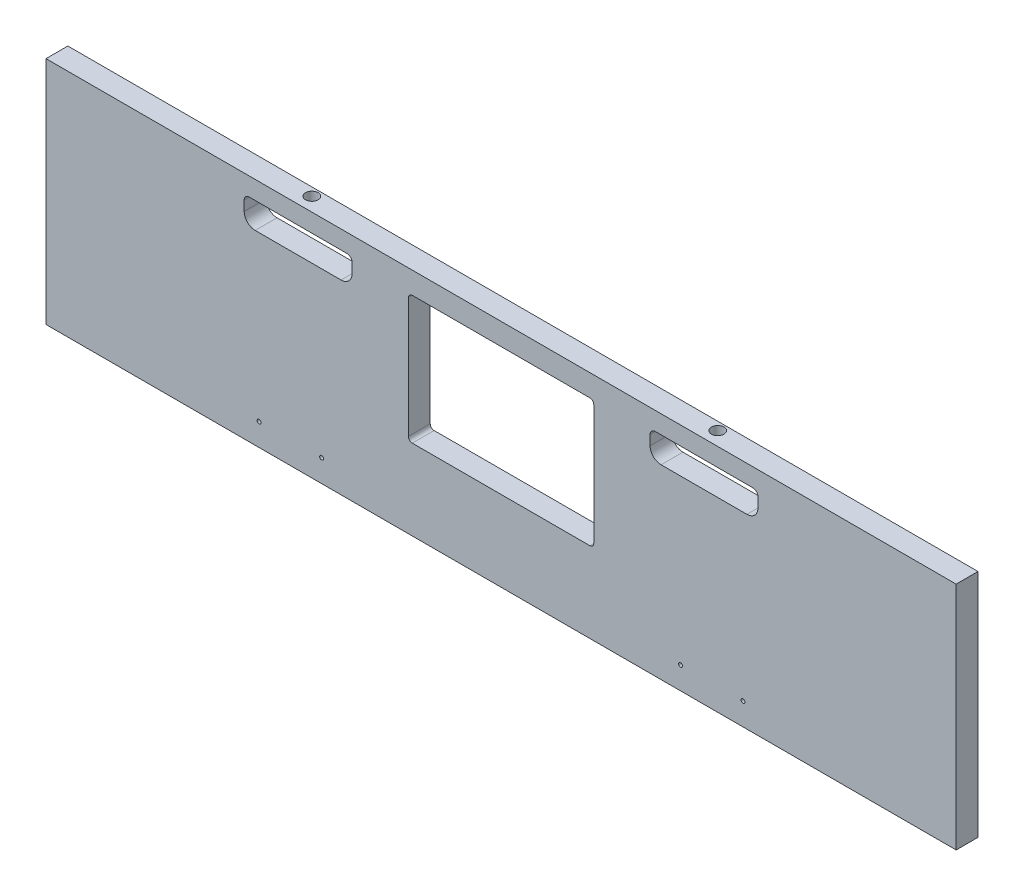
SolidWorks part; units mm, degrees
material "Pine"
ref_plane "Front Plane" through (0, 0, 0) normal (0, 0, 1) x (1, 0, 0)
ref_plane "Top Plane" through (0, 0, 0) normal (0, 1, 0) x (1, 0, 0)
ref_plane "Right Plane" through (0, 0, 0) normal (1, 0, 0) x (0, 0, -1)
sketch "Sketch1" plane through (0, 0, 0) normal (0, 0, 1) x (1, 0, 0)
  line L0 (-163.9887, -5335.905) -> (-163.9887, -5432.425)
  line L1 (-102.87, -5350.891) -> (-33.02, -5350.891)
  line L2 (-111.8235, -5341.9375) -> (-111.8235, -5334)
  line L3 (-24.0665, -5341.9375) -> (-24.0665, -5334)
  line L4 (-298.9262, -5332.73) -> (-167.1637, -5332.73)
  line L5 (-167.1637, -5435.6) -> (-298.9262, -5435.6)
  line L6 (-302.1012, -5432.425) -> (-302.1012, -5335.905)
  line L7 (-107.6325, -5329.809) -> (-28.2575, -5329.809)
  line L8 (174.9425, -5308.6) -> (174.9425, -5581.65)
  line L9 (449.2625, -5413.1661) -> (449.2625, -5421.9659)
  line L10 (595.3125, -5421.9659) -> (595.3125, -5413.1661)
  line L11 (839.47, -5509.5521) -> (839.47, -5307.6729)
  line L12 (839.47, -5307.6729) -> (863.6, -5307.6729)
  line L13 (839.47, -5509.5521) -> (863.6, -5509.5521)
  line L14 (863.6, -5509.5521) -> (863.6, -5307.6729)
  line L15 (-354.2665, -5341.9375) -> (-354.2665, -5334)
  line L16 (-100.8856, -5889.625) -> (-50.0856, -5889.625)
  line L17 (-104.0606, -5969) -> (-104.0606, -5892.8)
  line L18 (-46.9106, -5892.8) -> (-46.9106, -5969)
  line L19 (-50.0856, -5972.175) -> (-100.8856, -5972.175)
  line L20 (-100.8856, -5848.35) -> (-50.0856, -5848.35)
  line L21 (857.25, -5502.275) -> (157.1625, -5575.3)
  line L22 (857.25, -5314.95) -> (857.25, -5502.275)
  line L23 (157.1625, -5314.95) -> (157.1625, -5575.3)
  line L24 (857.25, -5314.95) -> (157.1625, -5314.95)
  line L25 (150.8125, -5308.6) -> (174.9425, -5308.6)
  line L26 (174.9425, -5581.65) -> (150.8125, -5581.65)
  line L27 (137.16, -5314.95) -> (137.16, -5502.275)
  line L28 (150.8125, -5581.65) -> (150.8125, -5308.6)
  line L29 (590.8224, -5408.676) -> (453.7526, -5408.676)
  line L30 (453.7526, -5426.456) -> (590.8224, -5426.456)
  line L31 (137.16, -6013.45) -> (137.16, -5867.4)
  line L32 (150.8125, -5746.75) -> (150.8125, -6019.8)
  line L33 (143.51, -5639.9938) -> (143.51, -5654.294)
  line L34 (590.8224, -5919.724) -> (453.7526, -5919.724)
  line L35 (453.7526, -5901.944) -> (590.8224, -5901.944)
  line L36 (449.2625, -5915.2339) -> (449.2625, -5906.4341)
  line L37 (174.9425, -6019.8) -> (174.9425, -5746.75)
  line L38 (595.3125, -5906.4341) -> (595.3125, -5915.2339)
  line L39 (839.47, -5818.8479) -> (839.47, -6020.7271)
  line L40 (839.47, -5818.8479) -> (863.6, -5818.8479)
  line L41 (863.6, -5818.8479) -> (863.6, -6020.7271)
  line L42 (839.47, -6020.7271) -> (863.6, -6020.7271)
  line L43 (-155.8782, -5867.4) -> (-603.25, -5867.4)
  line L44 (-433.07, -5350.891) -> (-363.22, -5350.891)
  line L45 (-437.8325, -5329.809) -> (-358.4575, -5329.809)
  line L46 (889, -6045.2) -> (-635, -6045.2)
  line L47 (-635, -5283.2) -> (889, -5283.2)
  line L48 (-635, -6045.2) -> (-635, -5283.2)
  line L49 (889, -5283.2) -> (889, -6045.2)
  line L50 (137.16, -5502.275) -> (-603.25, -5502.275)
  line L51 (-603.25, -5314.95) -> (137.16, -5314.95)
  line L52 (143.51, -5654.294) -> (-609.6, -5654.294)
  line L53 (-609.6, -5639.9938) -> (143.51, -5639.9938)
  line L54 (137.16, -5536.0062) -> (-603.25, -5536.0062)
  line L55 (-603.25, -5794.375) -> (137.16, -5794.375)
  line L56 (-603.25, -6013.45) -> (137.16, -6013.45)
  line L57 (-603.25, -5536.0062) -> (-603.25, -5794.375)
  line L58 (137.16, -5794.375) -> (137.16, -5536.0062)
  line L59 (-609.6, -5654.294) -> (-609.6, -5639.9938)
  line L60 (-603.25, -5867.4) -> (-603.25, -6013.45)
  line L61 (-603.25, -5314.95) -> (-603.25, -5502.275)
  line L62 (-442.0235, -5341.9375) -> (-442.0235, -5334)
  line L63 (857.25, -5826.125) -> (157.1625, -5753.1)
  line L64 (857.25, -6013.45) -> (857.25, -5826.125)
  line L65 (157.1625, -6013.45) -> (157.1625, -5753.1)
  line L66 (857.25, -6013.45) -> (157.1625, -6013.45)
  line L67 (174.9425, -5746.75) -> (150.8125, -5746.75)
  line L68 (150.8125, -6019.8) -> (174.9425, -6019.8)
  line L69 (137.16, -5867.4) -> (4.907, -5867.4)
  circle A0 centre (-36.195, -5484.0124) radius 1.5875
  arc A1 (-298.9262, -5332.73) -> (-302.1012, -5335.905) centre (-298.9262, -5335.905) ccw
  arc A2 (-302.1012, -5432.425) -> (-298.9262, -5435.6) centre (-298.9262, -5432.425) ccw
  arc A3 (-163.9887, -5335.905) -> (-167.1637, -5332.73) centre (-167.1637, -5335.905) ccw
  arc A4 (-167.1637, -5435.6) -> (-163.9887, -5432.425) centre (-167.1637, -5432.425) ccw
  arc A5 (-111.8235, -5341.9375) -> (-102.87, -5350.891) centre (-102.87, -5341.9375) ccw
  arc A6 (-107.6325, -5329.809) -> (-111.8235, -5334) centre (-107.6325, -5334) ccw
  circle A7 centre (166.0525, -5444.6613) radius 1.5875
  circle A8 centre (166.0525, -5358.1871) radius 1.5875
  circle A9 centre (471.4875, -5417.566) radius 1.5875
  arc A10 (453.7526, -5408.676) -> (449.2625, -5413.1661) centre (451.5076, -5410.9211) ccw
  arc A11 (449.2625, -5421.9659) -> (453.7526, -5426.456) centre (451.5076, -5424.2109) ccw
  circle A12 centre (522.2875, -5417.566) radius 1.5875
  circle A13 centre (573.0875, -5417.566) radius 1.5875
  arc A14 (590.8224, -5426.456) -> (595.3125, -5421.9659) centre (593.0674, -5424.2109) ccw
  arc A15 (595.3125, -5413.1661) -> (590.8224, -5408.676) centre (593.0674, -5410.9211) ccw
  circle A16 centre (848.36, -5471.8269) radius 1.5875
  circle A17 centre (848.36, -5409.0762) radius 1.5875
  circle A18 centre (848.36, -5346.3254) radius 1.5875
  arc A19 (-363.22, -5350.891) -> (-354.2665, -5341.9375) centre (-363.22, -5341.9375) ccw
  arc A20 (-354.2665, -5334) -> (-358.4575, -5329.809) centre (-358.4575, -5334) ccw
  arc A21 (-24.0665, -5334) -> (-28.2575, -5329.809) centre (-28.2575, -5334) ccw
  arc A22 (-33.02, -5350.891) -> (-24.0665, -5341.9375) centre (-33.02, -5341.9375) ccw
  circle A23 centre (-86.995, -5484.0124) radius 1.5875
  circle A24 centre (-333.4544, -5894.07) radius 2.54
  circle A25 centre (-333.4544, -5994.4) radius 2.54
  arc A26 (-104.0606, -5969) -> (-100.8856, -5972.175) centre (-100.8856, -5969) ccw
  arc A27 (-50.0856, -5972.175) -> (-46.9106, -5969) centre (-50.0856, -5969) ccw
  arc A28 (-100.8856, -5848.35) -> (-128.3819, -5857.875) centre (-100.8856, -5892.8) ccw
  arc A29 (-155.8782, -5867.4) -> (-128.3819, -5857.875) centre (-155.8782, -5822.95) ccw
  arc A30 (-22.5893, -5857.875) -> (-50.0856, -5848.35) centre (-50.0856, -5892.8) ccw
  circle A31 centre (-132.6356, -5894.07) radius 2.54
  circle A32 centre (-132.6356, -5994.4) radius 2.54
  arc A33 (-46.9106, -5892.8) -> (-50.0856, -5889.625) centre (-50.0856, -5892.8) ccw
  arc A34 (-100.8856, -5889.625) -> (-104.0606, -5892.8) centre (-100.8856, -5892.8) ccw
  arc A35 (-22.5893, -5857.875) -> (4.907, -5867.4) centre (4.907, -5822.95) ccw
  circle A36 centre (166.0525, -5531.1356) radius 1.5875
  arc A37 (449.2625, -5915.2339) -> (453.7526, -5919.724) centre (451.5076, -5917.4789) ccw
  arc A38 (453.7526, -5901.944) -> (449.2625, -5906.4341) centre (451.5076, -5904.1891) ccw
  circle A39 centre (166.0525, -5797.2644) radius 1.5875
  circle A40 centre (166.0525, -5883.7387) radius 1.5875
  circle A41 centre (166.0525, -5970.2129) radius 1.5875
  circle A42 centre (471.4875, -5910.834) radius 1.5875
  circle A43 centre (522.2875, -5910.834) radius 1.5875
  circle A44 centre (573.0875, -5910.834) radius 1.5875
  arc A45 (595.3125, -5906.4341) -> (590.8224, -5901.944) centre (593.0674, -5904.1891) ccw
  arc A46 (590.8224, -5919.724) -> (595.3125, -5915.2339) centre (593.0674, -5917.4789) ccw
  circle A47 centre (848.36, -5919.3238) radius 1.5875
  circle A48 centre (848.36, -5982.0746) radius 1.5875
  circle A49 centre (848.36, -5856.5731) radius 1.5875
  arc A50 (-437.8325, -5329.809) -> (-442.0235, -5334) centre (-437.8325, -5334) ccw
  circle A51 centre (-429.895, -5484.0124) radius 1.5875
  arc A52 (-442.0235, -5341.9375) -> (-433.07, -5350.891) centre (-433.07, -5341.9375) ccw
  circle A53 centre (-379.095, -5484.0124) radius 1.5875
sketch "Sketch2" plane through (0, 0, 0) normal (0, 0, 1) x (1, 0, 0)
  line L0 (137.16, -5502.275) -> (137.16, -5314.95)
  line L1 (137.16, -5314.95) -> (-603.25, -5314.95)
  line L2 (-603.25, -5314.95) -> (-603.25, -5502.275)
  line L3 (-603.25, -5502.275) -> (137.16, -5502.275)
extrude "Extrude1" add sketch "Sketch2" against normal blind 17.78
sketch "Sketch3" plane through (0, 0, 0) normal (0, 0, 1) x (1, 0, 0)
  line L0 (-308.4512, -5335.905) -> (-308.4512, -5433.695)
  line L1 (-305.2762, -5436.87) -> (-160.8137, -5436.87)
  line L2 (-157.6387, -5433.695) -> (-157.6387, -5335.905)
  line L3 (-160.8137, -5332.73) -> (-305.2762, -5332.73)
  line L4 (-354.2665, -5334) -> (-354.2665, -5341.9375)
  line L5 (-363.22, -5350.891) -> (-433.07, -5350.891)
  line L6 (-442.0235, -5341.9375) -> (-442.0235, -5334)
  line L7 (-437.8325, -5329.809) -> (-358.4575, -5329.809)
  line L8 (-102.87, -5350.891) -> (-33.02, -5350.891)
  line L9 (-24.0665, -5341.9375) -> (-24.0665, -5334)
  line L10 (-28.2575, -5329.809) -> (-107.6325, -5329.809)
  line L11 (-111.8235, -5334) -> (-111.8235, -5341.9375)
  line L12 (-148.1137, -5332.73) -> (-317.9762, -5332.73) construction
  line L16 (-157.6387, -5461.3175) -> (-157.6387, -5332.73) construction
  line L17 (-308.4512, -5332.73) -> (-308.4512, -5461.3175) construction
  line L21 (-420.37, -5436.87) -> (-45.72, -5436.87) construction
  line L22 (-398.145, -5329.809) -> (-398.145, -5314.95) construction
  line L23 (137.16, -5314.95) -> (-603.25, -5314.95) construction
  line L24 (-398.145, -5329.809) -> (-398.145, -5350.891) construction
  arc A0 (-308.4512, -5433.695) -> (-305.2762, -5436.87) centre (-305.2762, -5433.695) ccw
  arc A1 (-160.8137, -5436.87) -> (-157.6387, -5433.695) centre (-160.8137, -5433.695) ccw
  arc A2 (-157.6387, -5335.905) -> (-160.8137, -5332.73) centre (-160.8137, -5335.905) ccw
  arc A3 (-305.2762, -5332.73) -> (-308.4512, -5335.905) centre (-305.2762, -5335.905) ccw
  arc A4 (-354.2665, -5341.9375) -> (-363.22, -5350.891) centre (-363.22, -5341.9375) cw
  arc A5 (-433.07, -5350.891) -> (-442.0235, -5341.9375) centre (-433.07, -5341.9375) cw
  arc A6 (-442.0235, -5334) -> (-437.8325, -5329.809) centre (-437.8325, -5334) cw
  arc A7 (-358.4575, -5329.809) -> (-354.2665, -5334) centre (-358.4575, -5334) cw
  arc A8 (-33.02, -5350.891) -> (-24.0665, -5341.9375) centre (-33.02, -5341.9375) ccw
  arc A9 (-24.0665, -5334) -> (-28.2575, -5329.809) centre (-28.2575, -5334) ccw
  arc A10 (-107.6325, -5329.809) -> (-111.8235, -5334) centre (-107.6325, -5334) ccw
  arc A11 (-111.8235, -5341.9375) -> (-102.87, -5350.891) centre (-102.87, -5341.9375) ccw
  circle A12 centre (-429.895, -5484.0124) radius 1.5875
  circle A13 centre (-379.095, -5484.0124) radius 1.5875
  circle A14 centre (-86.995, -5484.0124) radius 1.5875
  circle A15 centre (-36.195, -5484.0124) radius 1.5875
  point P16 (-509.5773, -5301.4203)
  dimension "D1" = 21.082
  dimension "D2" = 14.859
extrude "Cut-Extrude1" cut sketch "Sketch3" against normal up to surface (17.78 mm away) up to face at (-233.045, -5408.6125, -17.78)
sketch "Sketch4" plane through (0, -5314.95, 0) normal (0, 1, 0) x (1, 0, 0)
  circle A0 centre (-67.97, 11.1873) radius 5.08
  circle A1 centre (-398.17, 11.1873) radius 5.08
extrude "Cut-Extrude2" cut sketch "Sketch4" against normal up to surface (14.859 mm away) up to face at (-67.945, -5329.809, -8.89)
